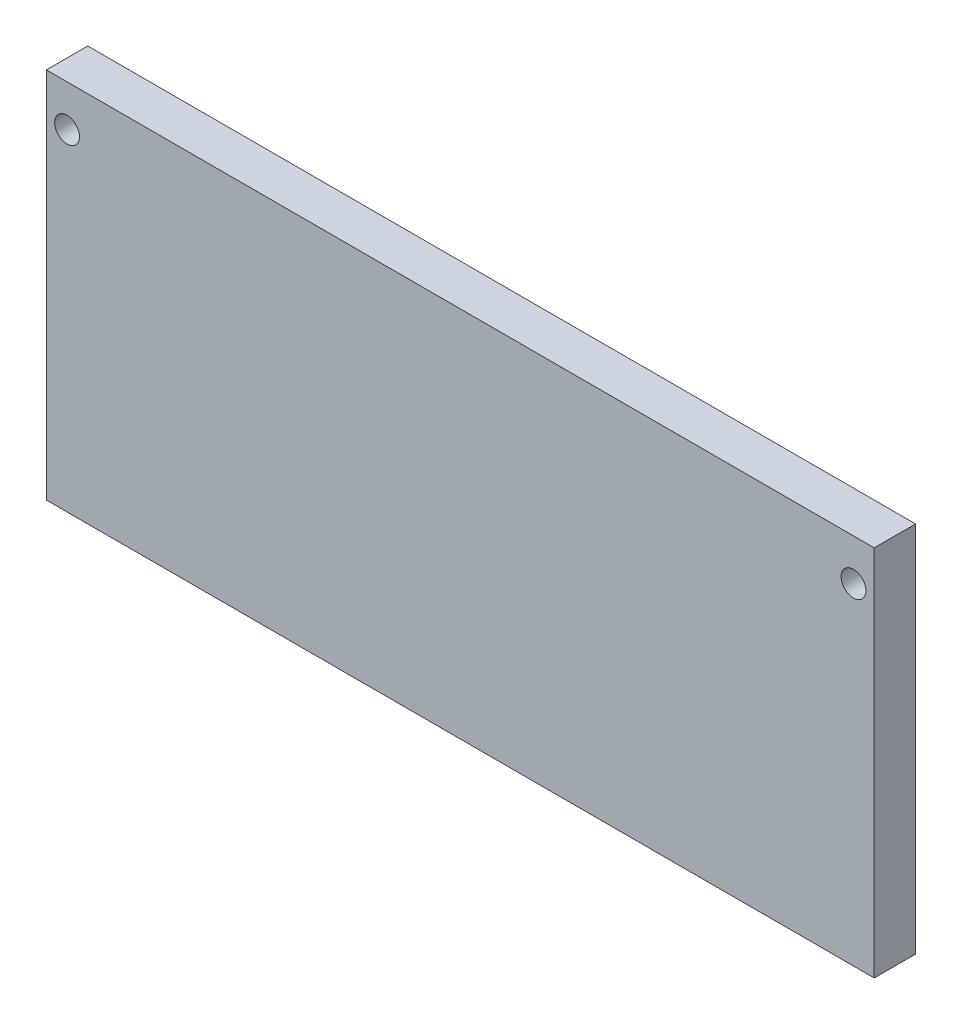
SolidWorks part; units mm, degrees
ref_plane "Front Plane" through (0, 0, 0) normal (0, 0, 1) x (1, 0, 0)
ref_plane "Top Plane" through (0, 0, 0) normal (0, 1, 0) x (1, 0, 0)
ref_plane "Right Plane" through (0, 0, 0) normal (1, 0, 0) x (0, 0, -1)
sketch "Sketch1" plane through (0, 0, 0) normal (0, 0, 1) x (1, 0, 0)
  line L1 (0, 0) -> (100, 0)
  line L2 (0, 0) -> (0, 45)
  line L3 (0, 45) -> (100, 45)
  line L4 (100, 0) -> (100, 45)
  circle A0 centre (2.5, 40) radius 1.5
  circle A1 centre (97.5, 40) radius 1.5
  dimension "D3" = 5
  dimension "D4" = 2.5
  dimension "D5" = 3
  dimension "D1" = 100
  dimension "D2" = 45
  dimension "D6" = 2
extrude "Boss-Extrude1" add sketch "Sketch1" along normal blind 5
